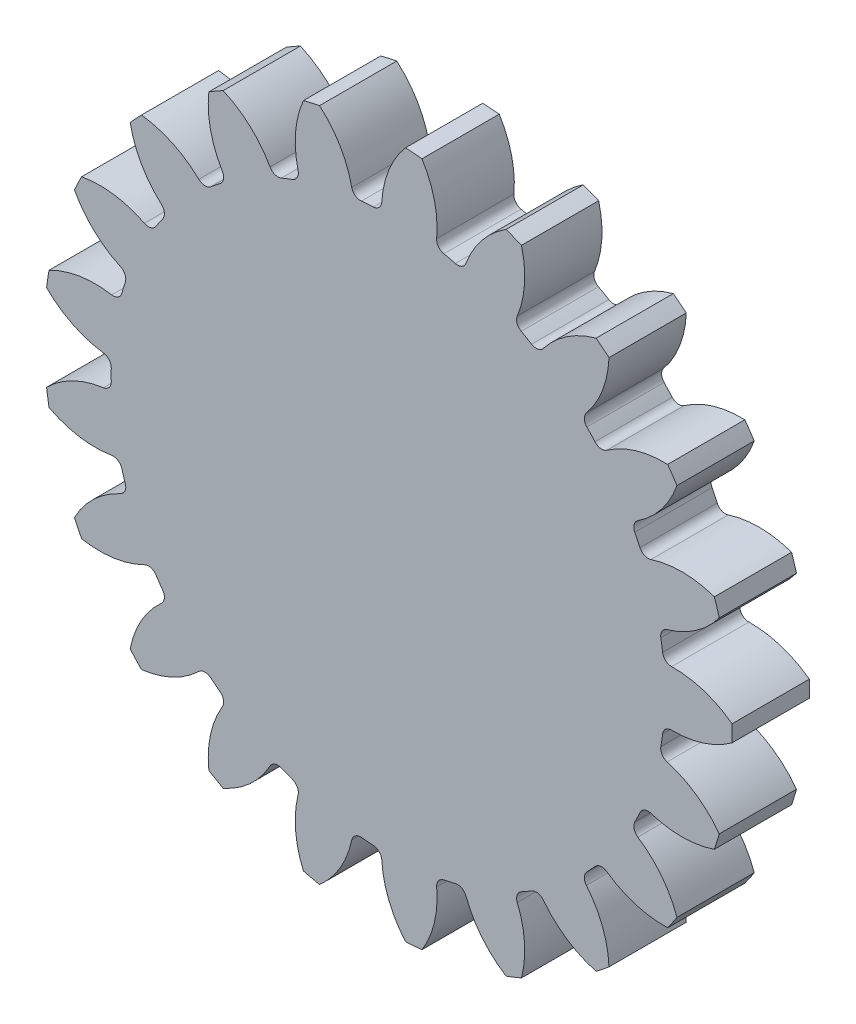
SolidWorks part; units mm, degrees
ref_plane "Front Plane" through (0, 0, 0) normal (0, 0, 1) x (1, 0, 0)
ref_plane "Top Plane" through (0, 0, 0) normal (0, 1, 0) x (1, 0, 0)
ref_plane "Right Plane" through (0, 0, 0) normal (1, 0, 0) x (0, 0, -1)
sketch "Sketch1" plane through (0, 0, 0) normal (0, 0, 1) x (1, 0, 0)
  circle A0 centre (0, 0) radius 32.55
  circle A1 centre (0, 0) radius 35.65
  circle A2 centre (0, 0) radius 28.675
  dimension "D1" = 65.1
  dimension "D2" = 71.3
  dimension "D3" = 6.975
extrude "Boss-Extrude1" add sketch "Sketch1" along normal mid plane 8 contours A1
sketch "Sketch4" plane through (0, 0, 0) normal (0, 0, 1) x (1, 0, 0)
  line L0 (0, 0) -> (-35.65, 0) construction
  line L1 (-32.459, -2.4325) -> (-32.459, 2.4325) construction
  line L2 (0, 0) -> (-28.6367, -1.4809) construction
  line L3 (-27.2425, 0) -> (-36.4004, -4.2704) construction
  line L4 (0, 0) -> (-35.2518, 5.3134) construction
  line L5 (-32.459, 2.4325) -> (-31.7339, 7.2431) construction
  circle A0 centre (0, 0) radius 35.65 construction
  arc A1 (-36.2424, -5.451) -> (-28.6367, -1.4809) centre (-28.1046, -11.7704) cw
  arc A2 (-36.2424, 5.451) -> (-28.6367, 1.4809) centre (-28.1046, 11.7704) ccw
  arc A3 (-36.2424, 5.451) -> (-36.2424, -5.451) centre (0, 0) ccw
  circle A4 centre (0, 0) radius 28.675
  arc A5 (-28.6367, 1.4809) -> (-28.6367, -1.4809) centre (0, 0) ccw
  circle A6 centre (0, 0) radius 35.65
  arc A7 (-35.3694, -4.4642) -> (-35.3694, 4.4642) centre (0, 0) ccw
  circle A10 centre (0, 0) radius 36.65 construction
  circle A11 centre (0, 0) radius 35.65 construction
  circle A15 centre (0, 0) radius 32.55
  circle A16 centre (0, 0) radius 32.55
  point P20 (32.9925, 10.0868)
  point P22 (35.5, 0)
  dimension "D4" = 25
  dimension "D5" = 8.571
  dimension "D2" = 0
  dimension "D3" = 1
  dimension "D6" = 0
extrude "Cut-Extrude1" cut sketch "Sketch4" against normal through all both and the other way through all contours A16 A2 A3 A1 | A2 A16 A1 A5
fillet "Fillet1" radius 0.93 2 edges at (-28.6367, -1.4809, 0) (-28.6367, 1.4809, 0)
pattern_circular "CirPattern1" count 21 over 360 about axis through (0, 0, 0) along (0, 0, 1) of "Cut-Extrude1", "Fillet1"
sketch "Sketch5" plane through (0, 0, 4) normal (0, 0, 1) x (1, 0, 0)
  circle A0 centre (0, 0) radius 2.9
  dimension "D1" = 5.8
equation "\"Module\"= 3.1mm"
equation "\"Number of Teeth\" = 21"
equation "\"D1@Sketch1\"=\"Module\" * \"Number of Teeth\""
equation "\"D2@Sketch1\"=(\"Number of Teeth\" + 2) * \"Module\""
equation "\"D3@Sketch1\"=\"Module\" * if(\"Module\"=>1.25,2.25,2.4)"
equation "\"D5@Sketch4\"=180 / \"Number of Teeth\""
equation "\"D1@Fillet1\"=.3 * \"Module\""
equation "\"D1@CirPattern1\"=\"Number of Teeth\""
